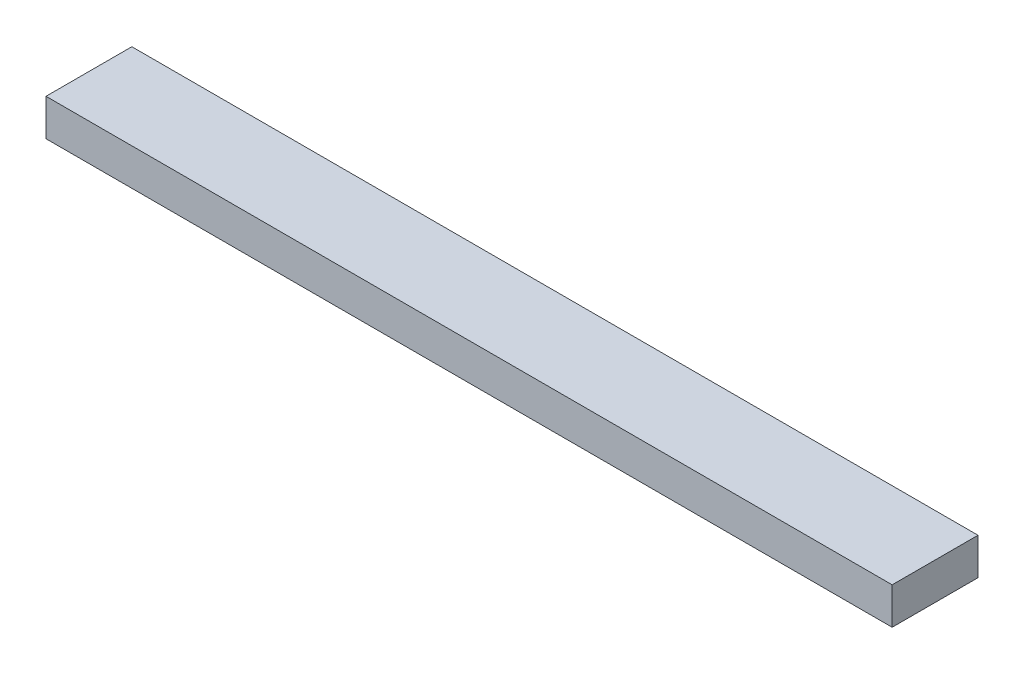
SolidWorks part; units mm, degrees
ref_plane "Front Plane" through (0, 0, 0) normal (0, 0, 1) x (1, 0, 0)
ref_plane "Top Plane" through (0, 0, 0) normal (0, 1, 0) x (1, 0, 0)
ref_plane "Right Plane" through (0, 0, 0) normal (1, 0, 0) x (0, 0, -1)
sketch "Sketch1" plane through (0, 0, 0) normal (0, 1, 0) x (1, 0, 0)
  line L1 (0, 0) -> (876.3, 0)
  line L2 (0, 0) -> (0, 88.9)
  line L3 (0, 88.9) -> (876.3, 88.9)
  line L4 (876.3, 0) -> (876.3, 88.9)
  dimension "D1" = 88.9
  dimension "D2" = 876.3
extrude "Boss-Extrude1" add sketch "Sketch1" along normal blind 38.1
